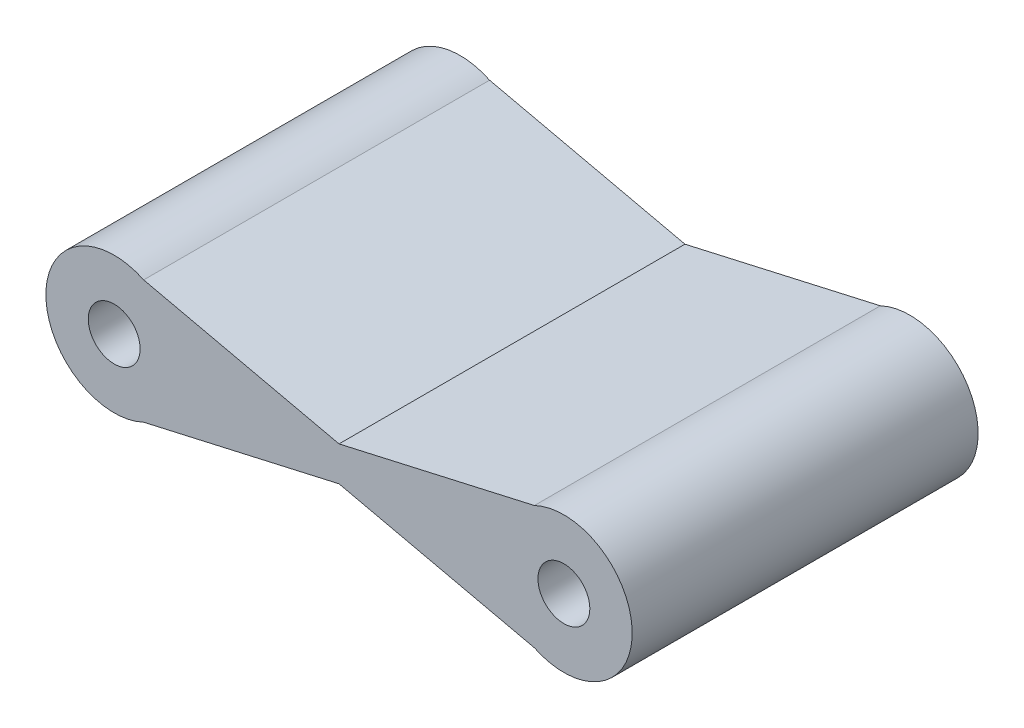
SolidWorks part; units mm, degrees
ref_plane "Front Plane" through (0, 0, 0) normal (0, 0, 1) x (1, 0, 0)
ref_plane "Top Plane" through (0, 0, 0) normal (0, 1, 0) x (1, 0, 0)
ref_plane "Right Plane" through (0, 0, 0) normal (1, 0, 0) x (0, 0, -1)
sketch "Sketch1" plane through (0, 0, 0) normal (0, 0, 1) x (1, 0, 0)
  line L0 (0, 2.475) -> (6.5, 1)
  line L1 (0, 1) -> (13, 1)
  line L2 (0, 1) -> (0, 0)
  line L3 (0, 0) -> (13, 0)
  line L4 (13, 1) -> (13, 0)
  line L5 (6.5, 1) -> (13, 2.475)
  line L6 (13, -1.475) -> (6.5, 0)
  line L7 (0, -1.475) -> (6.5, 0)
  circle A0 centre (0, 0.5) radius 1.975
  circle A1 centre (13, 0.5) radius 1.975
  circle A2 centre (0, 0.5) radius 0.75
  circle A3 centre (13, 0.5) radius 0.75
  dimension "D3" = 3.95
  dimension "D4" = 1.5
  dimension "D1" = 1
  dimension "D2" = 13
extrude "Boss-Extrude1" add sketch "Sketch1" along normal blind 10 contours L1 A0 L0 L7 L3 L2 | L3 A0 L1 L2 | A1 L1 A0 L3 | A0 L1 L0 | A1 L5 L1 | L5 A1 L1 L4 L3 L6 | L1 A1 L3 L4 | A1 L3 L6 | A0 L7 L3 | L5 A1 | L6 A1 | L7 A0 | L0 A0
